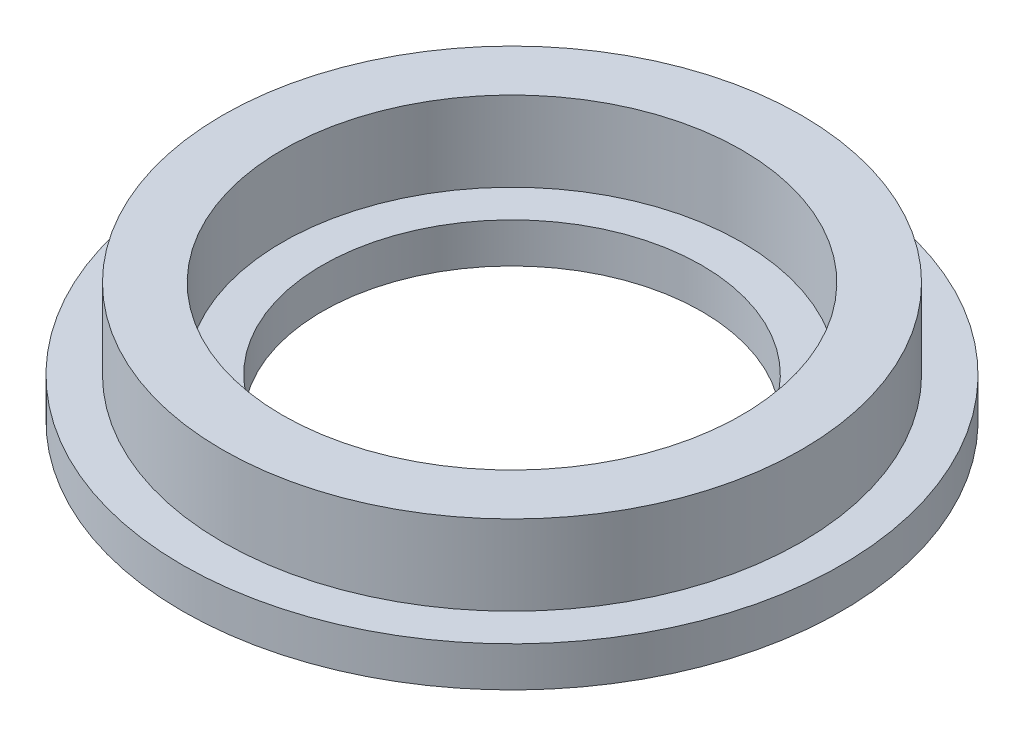
SolidWorks part; units mm, degrees
material "ABS"
ref_plane "Ebene vorne" through (0, 0, 0) normal (0, 0, 1) x (1, 0, 0)
ref_plane "Ebene oben" through (0, 0, 0) normal (0, 1, 0) x (1, 0, 0)
ref_plane "Ebene rechts" through (0, 0, 0) normal (1, 0, 0) x (0, 0, -1)
sketch "Skizze1" plane through (0, 0, 0) normal (0, 0, 1) x (1, 0, 0)
  line L0 (0, 0) -> (0, 181.78) construction
  line L1 (-9.5, 0) -> (-16.5, 0)
  line L2 (-16.5, 0) -> (-16.5, 2)
  line L3 (-16.5, 2) -> (-14.5, 2)
  line L4 (-14.5, 2) -> (-14.5, 6)
  line L5 (-14.5, 6) -> (-11.5, 6)
  line L6 (-9.5, 2) -> (-9.5, 0)
  line L7 (-9.5, 2) -> (-11.5, 2)
  line L8 (-11.5, 2) -> (-11.5, 6)
  dimension "D1" = 11.5
  dimension "D2" = 4
  dimension "D3" = 2
  dimension "D4" = 3
  dimension "D5" = 2
  dimension "D6" = 2
revolve "Rotation1" add sketch "Skizze1" angle 360 about L0
